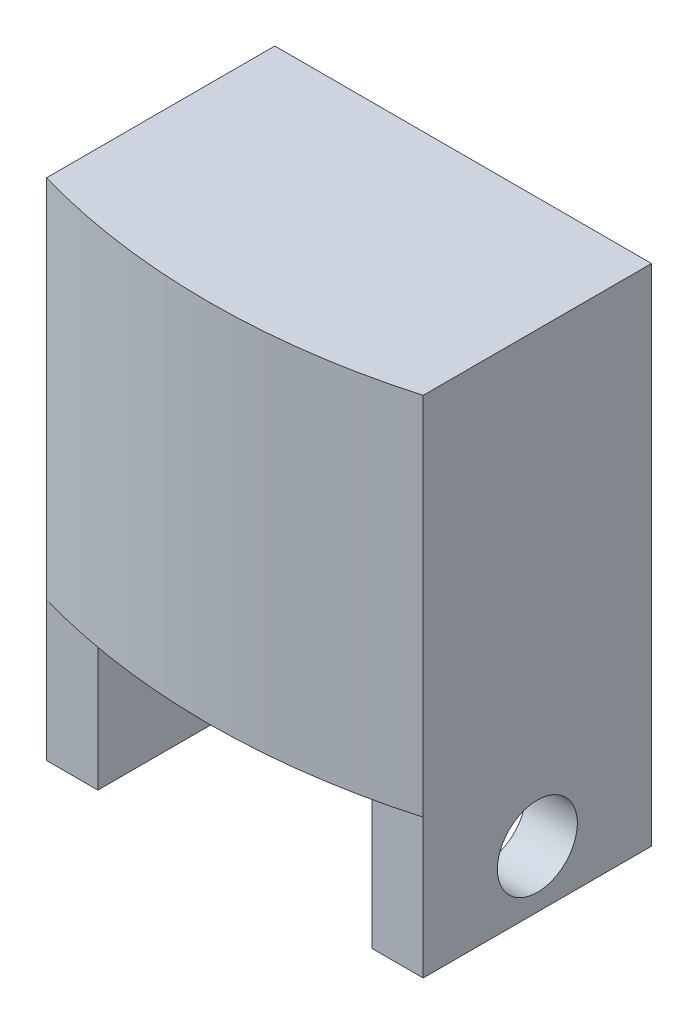
SolidWorks part; units mm, degrees
ref_plane "Front Plane" through (0, 0, 0) normal (0, 0, 1) x (1, 0, 0)
ref_plane "Top Plane" through (0, 0, 0) normal (0, 1, 0) x (1, 0, 0)
ref_plane "Right Plane" through (0, 0, 0) normal (1, 0, 0) x (0, 0, -1)
sketch "Sketch1" plane through (0, 0, 0) normal (0, 1, 0) x (1, 0, 0)
  line L0 (-16.5, 10) -> (16.5, 10)
  line L1 (16.5, 10) -> (16.5, -10)
  line L2 (-16.5, 10) -> (-16.5, -10)
  arc A0 (-16.5, -10) -> (16.5, -10) centre (0, 47.6867) ccw
  point P5 (0, 10)
  point P7 (-16.5, 0)
  dimension "D3" = 60
  dimension "D1" = 33
  dimension "D2" = 20
extrude "Boss-Extrude1" add sketch "Sketch1" along normal blind 32 contours A0 L1 L0 L2
sketch "Sketch3" plane through (-16.5, 0, 0) normal (-1, 0, 0) x (0, 0, 1)
  line L0 (-10, 0) -> (-10, -12.2)
  line L1 (-10, -12.2) -> (10, -12.2)
  line L2 (10, -12.2) -> (10, 0)
  line L3 (10, 0) -> (-10, 0)
  dimension "D1" = 12.2
extrude "Boss-Extrude2" add sketch "Sketch3" against normal blind 4.5
mirror "Mirror1" about plane through (0, 0, 0) normal (1, 0, 0) of "Boss-Extrude2"
sketch "Sketch4" plane through (-16.5, 0, 0) normal (-1, 0, 0) x (0, 0, 1)
  line L0 (-10, -12.2) -> (10, -12.2) construction
  circle A0 centre (0, -7.2) radius 3.5
  dimension "D1" = 7
  dimension "D2" = 5
extrude "Cut-Extrude1" cut sketch "Sketch4" against normal through all
sketch "Sketch5" plane through (-16.5, 0, 0) normal (-1, 0, 0) x (0, 0, 1)
  line L0 (-10, 32) -> (10, 32) construction
  circle A0 centre (0, 24.5) radius 3.5
  dimension "D1" = 7
  dimension "D2" = 7.5
extrude "Cut-Extrude2" cut sketch "Sketch5" against normal blind 9
fillet "Fillet1" radius 2.5 2 edges at (12, -6.1, -10)
